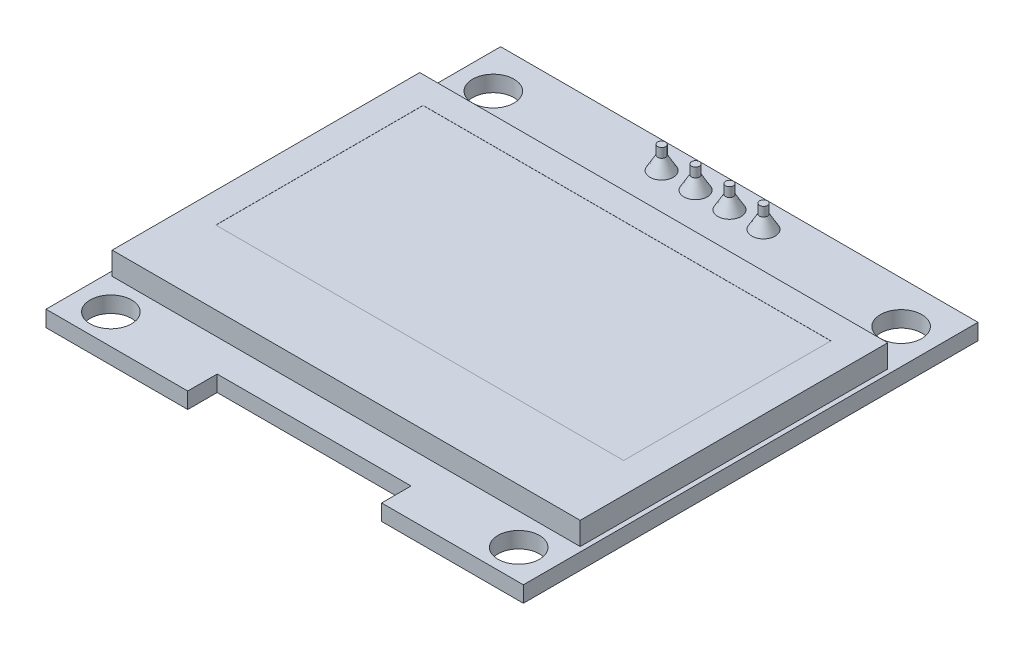
SolidWorks part; units mm, degrees
ref_plane "Ebene vorne" through (0, 0, 0) normal (0, 0, 1) x (1, 0, 0)
ref_plane "Ebene oben" through (0, 0, 0) normal (0, 1, 0) x (1, 0, 0)
ref_plane "Ebene rechts" through (0, 0, 0) normal (1, 0, 0) x (0, 0, -1)
sketch "Skizze1" plane through (0, 0, 0) normal (0, 1, 0) x (1, 0, 0)
  line L1 (-17.85, -17) -> (17.85, -17)
  line L2 (-17.85, -17) -> (-17.85, 17)
  line L3 (-17.85, 17) -> (17.85, 17)
  line L4 (17.85, -17) -> (17.85, 17)
  line L5 (-17.85, -17) -> (17.85, 17) construction
  line L6 (-17.85, 17) -> (17.85, -17) construction
  point P0 (0, 0)
  dimension "D1" = 35.7
  dimension "D2" = 34
extrude "Aufsatz-Linear austragen1" add sketch "Skizze1" along normal blind 1.2
sketch "Skizze2" plane through (0, 1.2, 0) normal (0, 1, 0) x (1, 0, 0)
  line L0 (0, 17) -> (0, -17) construction
  line L1 (17.85, 17) -> (-17.85, 17) construction
  line L2 (-17.85, -17) -> (17.85, -17) construction
  circle A0 centre (-15.25, 13.85) radius 1.55
  circle A1 centre (15.25, 13.85) radius 1.55
  circle A2 centre (15.25, -14.75) radius 1.55
  circle A3 centre (-15.25, -14.75) radius 1.55
  point P8 (0, 0)
  point P9 (0, 0)
  point P20 (0, 0)
  point P21 (0, 0)
  dimension "D4" = 3.1
  dimension "D1" = 28.6
  dimension "D2" = 30.5
  dimension "D3" = 3.15
extrude "Schnitt-Linear austragen1" cut sketch "Skizze2" against normal through all
sketch "Skizze3" plane through (0, 1.2, 0) normal (0, 1, 0) x (1, 0, 0)
  line L0 (0, 0) -> (0, 10.6) construction
  line L1 (-17.5, 10.6) -> (17.5, 10.6)
  line L2 (-17.5, 10.6) -> (-17.5, -12.4)
  line L3 (-17.5, -12.4) -> (17.5, -12.4)
  line L4 (17.5, 10.6) -> (17.5, -12.4)
  line L5 (17.85, 17) -> (-17.85, 17) construction
  dimension "D1" = 35
  dimension "D2" = 23
  dimension "D3" = 6.4
extrude "Aufsatz-Linear austragen2" add sketch "Skizze3" along normal blind 1.7
sketch "Skizze4" plane through (0, 2.9, 0) normal (0, 1, 0) x (1, 0, 0)
  line L0 (0, 0) -> (0, 8.6) construction
  line L1 (-15.25, 8.6) -> (15.25, 8.6)
  line L2 (-15.25, 8.6) -> (-15.25, -6.9)
  line L3 (-15.25, -6.9) -> (15.25, -6.9)
  line L4 (15.25, 8.6) -> (15.25, -6.9)
  line L5 (17.5, 10.6) -> (-17.5, 10.6) construction
  dimension "D1" = 30.5
  dimension "D2" = 15.5
  dimension "D3" = 2
extrude "Schnitt-Linear austragen2" cut sketch "Skizze4" against normal blind 0.01
sketch "Skizze5" plane through (0, 1.2, 0) normal (0, 1, 0) x (1, 0, 0)
  line L0 (-17.85, -17) -> (17.85, -17) construction
  line L1 (-7.25, -17) -> (7.25, -17)
  line L2 (-7.25, -17) -> (-7.25, -14.8)
  line L3 (-7.25, -14.8) -> (7.25, -14.8)
  line L4 (7.25, -17) -> (7.25, -14.8)
  line L5 (0, 0) -> (0, -14.8) construction
  dimension "D1" = 14.5
  dimension "D2" = 2.2
extrude "Schnitt-Linear austragen3" cut sketch "Skizze5" against normal through all
sketch "Skizze6" plane through (0, 1.2, 0) normal (0, 1, 0) x (1, 0, 0)
  line L0 (17.85, 17) -> (-17.85, 17) construction
  line L1 (-3.81, 15) -> (3.81, 15) construction
  line L2 (0, 0) -> (0, 15) construction
  circle A0 centre (-3.81, 15) radius 0.875
  circle A1 centre (3.81, 15) radius 0.875
  circle A2 centre (1.27, 15) radius 0.875
  circle A3 centre (-1.27, 15) radius 0.875
  dimension "D5" = 1.75
  dimension "D1" = 2.54
  dimension "D2" = 2.54
  dimension "D3" = 2.54
  dimension "D4" = 2
extrude "Aufsatz-Linear austragen3" add sketch "Skizze6" along normal blind 1 draft 30
sketch "Skizze7" plane through (0, 2.2, 0) normal (0, 1, 0) x (1, 0, 0)
  circle A0 centre (-1.27, 15) radius 0.2976 construction
  circle A1 centre (-3.81, 15) radius 0.2976
  circle A2 centre (-3.81, 15) radius 0.2976
  circle A3 centre (1.27, 15) radius 0.2976 construction
  circle A4 centre (-1.27, 15) radius 0.2976
  circle A5 centre (1.27, 15) radius 0.2976
  circle A7 centre (3.81, 15) radius 0.2976
  circle A8 centre (3.81, 15) radius 0.2976
  dimension "D1" = 0
  dimension "D2" = 0
extrude "Aufsatz-Linear austragen4" add sketch "Skizze7" along normal blind 0.7
sketch "Skizze8" plane through (0, 0, 0) normal (0, -1, 0) x (1, 0, 0)
  circle A0 centre (-3.81, -15) radius 0.2976 construction
  circle A1 centre (-1.27, -15) radius 0.2976
  circle A2 centre (-1.27, -15) radius 0.2976
  circle A3 centre (1.27, -15) radius 0.2976 construction
  circle A4 centre (3.81, -15) radius 0.2976 construction
  circle A5 centre (-3.81, -15) radius 0.2976
  circle A6 centre (1.27, -15) radius 0.2976
  circle A7 centre (3.81, -15) radius 0.2976
  dimension "D1" = 0
extrude "Aufsatz-Linear austragen5" add sketch "Skizze8" along normal blind 8.5
sketch "Skizze9" plane through (0, 0, 0) normal (0, -1, 0) x (1, 0, 0)
  line L0 (-3.81, -15) -> (-5.05, -15) construction
  line L1 (-5.05, -13.73) -> (5.05, -13.73)
  line L2 (-5.05, -13.73) -> (-5.05, -16.27)
  line L3 (-5.05, -16.27) -> (5.05, -16.27)
  line L4 (5.05, -13.73) -> (5.05, -16.27)
  line L5 (-3.81, -15) -> (3.81, -15) construction
  line L6 (0, -15) -> (0, -13.73) construction
  dimension "D1" = 2.54
  dimension "10.1" = 10.1
extrude "Aufsatz-Linear austragen6" add sketch "Skizze9" along normal blind 1.8 separate body
equation "\"D1@Skizze2\"=31.7-3.1"
equation "\"D2@Skizze2\"=33.6-3.1"
equation "\"D3@Skizze2\"=1.6+1.55"
equation "\"D2@Skizze6\"=\"D1@Skizze6\""
equation "\"D3@Skizze6\"=\"D1@Skizze6\""
